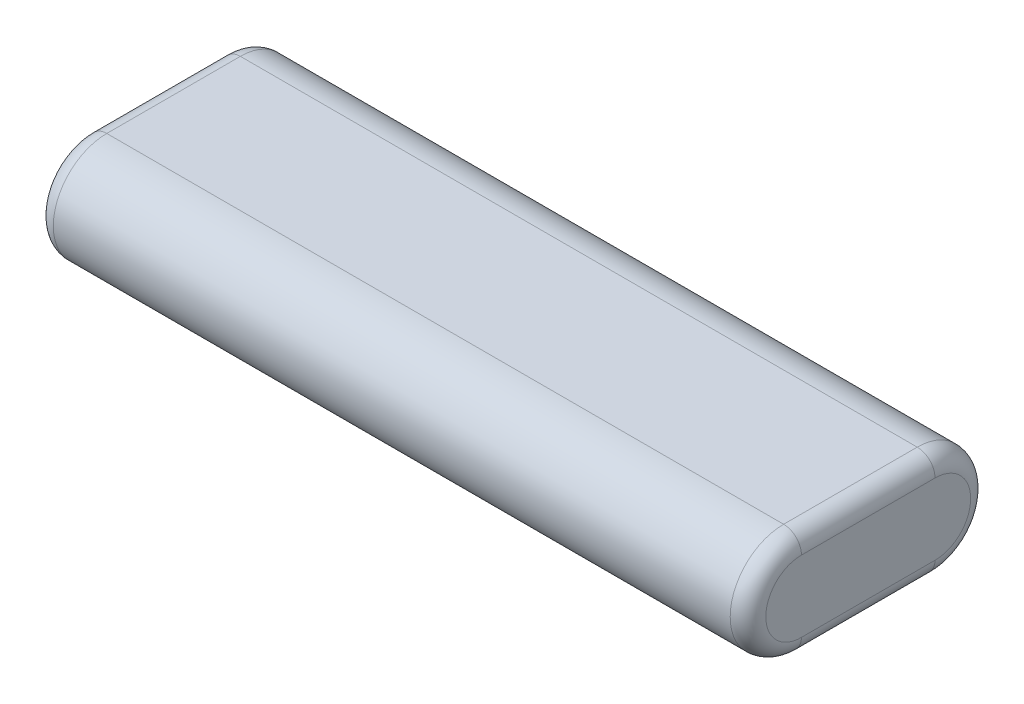
SolidWorks part; units mm, degrees
ref_plane "Front Plane" through (0, 0, 0) normal (0, 0, 1) x (1, 0, 0)
ref_plane "Top Plane" through (0, 0, 0) normal (0, 1, 0) x (1, 0, 0)
ref_plane "Right Plane" through (0, 0, 0) normal (1, 0, 0) x (0, 0, -1)
sketch "Sketch1" plane through (0, 0, 0) normal (1, 0, 0) x (0, 0, -1)
  line L0 (21.4313, 0) -> (-21.4312, 0) construction
  line L1 (-11.9062, -9.525) -> (11.9062, -9.525)
  line L2 (-11.9062, -9.525) -> (-11.9062, 9.525)
  line L3 (-11.9062, 9.525) -> (11.9062, 9.525)
  line L4 (11.9062, -9.525) -> (11.9062, 9.525)
  line L5 (-11.9062, -9.525) -> (11.9062, 9.525) construction
  line L6 (-11.9062, 9.525) -> (11.9062, -9.525) construction
  arc A0 (-11.9062, 9.525) -> (-11.9062, -9.525) centre (-11.9062, 0) ccw
  arc A1 (11.9062, 9.525) -> (11.9062, -9.525) centre (11.9062, 0) cw
  point P0 (0, 0)
  dimension "D1" = 42.8625
  dimension "D2" = 19.05
extrude "Boss-Extrude1" add sketch "Sketch1" along normal mid plane 127 contours L2 A0 | L1 L4 L3 L2 | A1 L4
fillet "Fillet1" radius 3.175 8 edges at (-63.5, -9.525, 0) (63.5, -9.525, 0) (-63.5, 0, -21.4312) (63.5, 0, -21.4312) (-63.5, 9.525, 0) (63.5, 9.525, 0) (-63.5, 0, 21.4312) (63.5, 0, 21.4312)
